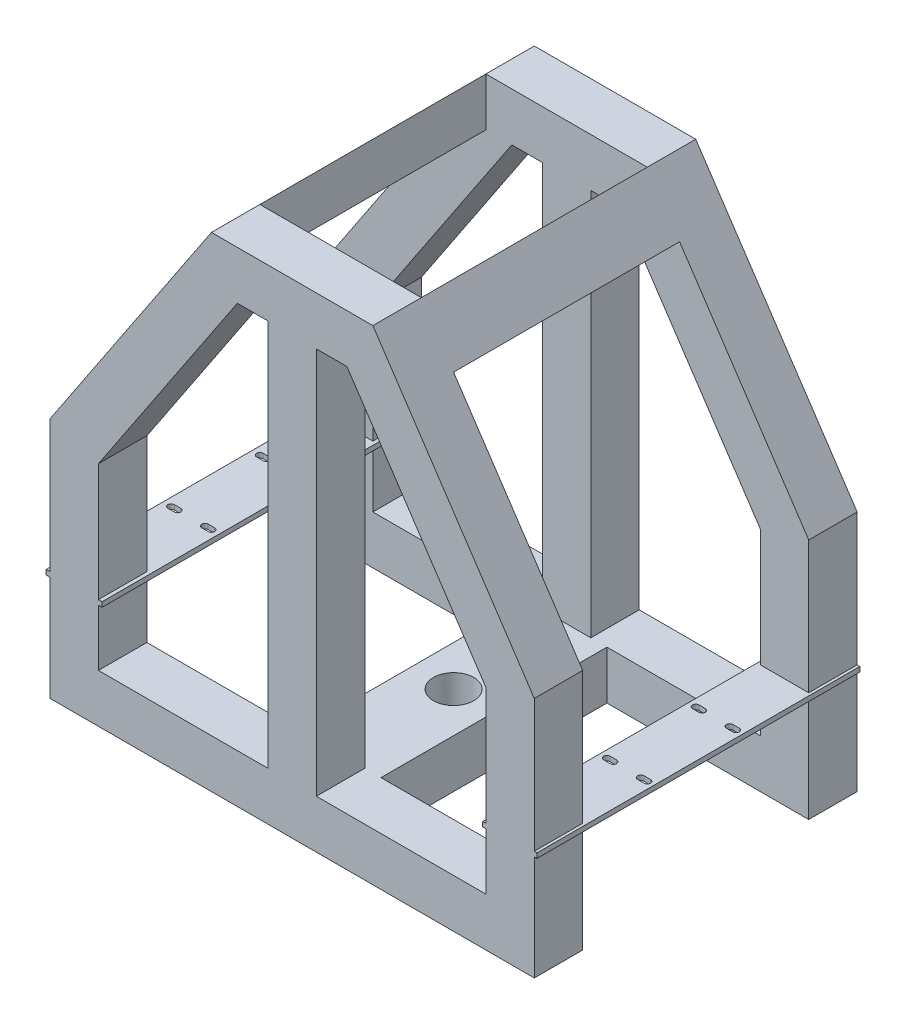
SolidWorks part; units mm, degrees
ref_plane "Front Plane" through (0, 0, 0) normal (0, 0, 1) x (1, 0, 0)
ref_plane "Top Plane" through (0, 0, 0) normal (0, 1, 0) x (1, 0, 0)
ref_plane "Right Plane" through (0, 0, 0) normal (1, 0, 0) x (0, 0, -1)
sketch "Sketch1" plane through (0, 0, 0) normal (0, 0, 1) x (1, 0, 0)
  line L0 (16.8622, -146.019) -> (16.8622, -177.0228) construction
  line L1 (66.8622, 153.981) -> (-33.1378, 153.981) construction
  line L2 (-33.1378, 153.981) -> (-133.1378, 3.981) construction
  line L3 (-133.1378, 3.981) -> (-133.1378, -146.019) construction
  line L4 (-133.1378, -146.019) -> (166.8622, -146.019) construction
  line L5 (1.8622, 153.981) -> (-33.1378, 153.981)
  line L6 (1.8622, -46.019) -> (31.8622, -46.019)
  line L7 (1.8622, -116.019) -> (1.8622, 123.981)
  line L8 (1.8622, 153.981) -> (31.8622, 153.981)
  line L9 (31.8622, -46.019) -> (31.8622, 153.981)
  line L10 (16.8622, 153.981) -> (16.8622, 166.0651) construction
  line L11 (16.8622, 166.0651) -> (16.8622, -345.3513) construction
  line L13 (-133.1378, 3.981) -> (-133.1378, -146.019)
  line L14 (-133.1378, -146.019) -> (-53.1378, -146.019)
  line L15 (-103.1378, -5.1022) -> (-103.1378, -116.019)
  line L16 (-33.1378, 153.981) -> (-133.1378, 3.981)
  line L17 (-133.1378, -146.019) -> (166.8622, -146.019)
  line L18 (166.8622, 3.981) -> (166.8622, -146.019) construction
  line L19 (66.8622, 153.981) -> (-33.1378, 153.981)
  line L20 (-17.0822, 123.981) -> (-103.1378, -5.1022)
  line L21 (1.8622, 123.981) -> (-17.0822, 123.981)
  line L22 (-103.1378, -5.1022) -> (-103.1378, -116.019)
  line L23 (-103.1378, -116.019) -> (1.8622, -116.019)
  line L24 (-8.1763, 137.34) -> (-108.1763, -12.66) construction
  line L25 (1.8622, 123.981) -> (-33.1378, 123.981) construction
  line L26 (-103.1378, 3.981) -> (-103.1378, -146.019) construction
  line L27 (66.8622, 153.981) -> (166.8622, 3.981) construction
  line L28 (136.8622, -116.019) -> (31.8622, -116.019)
  line L29 (136.8622, -5.1022) -> (136.8622, -116.019)
  line L30 (31.8622, 123.981) -> (50.8067, 123.981)
  line L31 (50.8067, 123.981) -> (136.8622, -5.1022)
  line L32 (66.8622, 153.981) -> (166.8622, 3.981)
  line L33 (136.8622, -5.1022) -> (136.8622, -116.019)
  line L34 (166.8622, -146.019) -> (86.8622, -146.019)
  line L35 (166.8622, 3.981) -> (166.8622, -146.019)
  line L36 (1.8622, -46.019) -> (1.8622, 153.981)
  line L37 (31.8622, -116.019) -> (31.8622, 123.981)
  line L38 (31.8622, 153.981) -> (66.8622, 153.981)
  point P4 (16.8622, -46.019)
  dimension "D1" = 150
  dimension "D2" = 150
  dimension "D3" = 150
  dimension "D4" = 150
  dimension "D5" = 50
  dimension "D6" = 30
  dimension "D9" = 30
  dimension "D8" = 30
extrude "Boss-Extrude4" add sketch "Sketch1" along normal blind 200 contours L28 L37 L6 L7 L23 L15 L20 L21 L36 L5 L16 L13 L14 L17 L35 L32 L19 L9 L30 L31 L29 | L36 L7 L6 L9 L8
sketch "Sketch5" plane through (0, -146.019, 0) normal (0, -1, 0) x (1, 0, 0)
  line L0 (-133.1378, 200) -> (-133.1378, 0) construction
  line L1 (-133.1378, 170) -> (166.8622, 170)
  line L2 (-133.1378, 170) -> (-133.1378, 30)
  line L3 (-133.1378, 30) -> (166.8622, 30)
  line L4 (166.8622, 170) -> (166.8622, 30)
  line L5 (166.8622, 200) -> (166.8622, 0) construction
  line L6 (-133.1378, 200) -> (166.8622, 200) construction
  line L7 (-133.1378, 0) -> (166.8622, 0) construction
  dimension "D1" = 30
  dimension "D2" = 30
extrude "Cut-Extrude3" cut sketch "Sketch5" against normal blind 270
sketch "Sketch6" plane through (0, 0, 200) normal (0, 0, 1) x (1, 0, 0)
  line L0 (-133.1378, 3.981) -> (-133.1378, -146.019) construction
  line L1 (-133.1378, -81.019) -> (-103.1378, -81.019)
  line L3 (-133.1378, -78.019) -> (-103.1378, -78.019)
  line L5 (-103.1378, -5.1022) -> (-103.1378, -116.019) construction
  line L6 (136.8622, -5.1022) -> (136.8622, -116.019) construction
  line L7 (136.8622, -81.019) -> (166.8622, -81.019)
  line L9 (136.8622, -78.019) -> (166.8622, -78.019)
  line L11 (166.8622, 3.981) -> (166.8622, -146.019) construction
  line L12 (-133.1378, -146.019) -> (166.8622, -146.019) construction
  line L14 (-135.5496, -78.019) -> (-100.8938, -78.019)
  line L15 (-135.5496, -78.019) -> (-135.5496, -81.019)
  line L16 (-135.5496, -81.019) -> (-100.8938, -81.019)
  line L17 (-100.8938, -78.019) -> (-100.8938, -81.019)
  line L18 (134.9079, -78.019) -> (168.5403, -78.019)
  line L19 (134.9079, -78.019) -> (134.9079, -81.019)
  line L20 (134.9079, -81.019) -> (168.5403, -81.019)
  line L21 (168.5403, -78.019) -> (168.5403, -81.019)
  point P18 (151.8622, -78.019)
  line M8 (136.8622, -5.1022) -> (136.8622, -116.019)
  line M13 (-133.1378, 3.981) -> (-133.1378, -146.019)
  line M15 (166.8622, -146.019) -> (166.8622, 3.981)
  line M19 (-103.1378, -116.019) -> (-103.1378, -5.1022)
  dimension "D1" = 68
  dimension "D2" = 68
  dimension "D3" = 3
  dimension "D4" = 3
extrude "Boss-Extrude6" add sketch "Sketch6" against normal blind 200 contours L15 L16 L14 M13 | L3 L1 M13 M19 | L17 L14 L16 M19 | L9 L7 M8 M15 | L21 L18 L20 M15 | L19 L20 L18 M8
sketch "Sketch7" plane through (0, 153.981, 0) normal (0, 1, 0) x (1, 0, 0)
  line L0 (-33.1378, -200) -> (-33.1378, 0) construction
  line L1 (-33.1378, -30) -> (66.8622, -30)
  line L2 (-33.1378, -30) -> (-33.1378, -170)
  line L3 (-33.1378, -170) -> (66.8622, -170)
  line L4 (66.8622, -30) -> (66.8622, -170)
  line L5 (66.8622, -200) -> (66.8622, 0) construction
extrude "Cut-Extrude4" cut sketch "Sketch7" against normal blind 174
sketch "Sketch9" plane through (0, 0, 0) normal (0, 0, -1) x (-1, 0, 0)
  line L0 (-136.8622, -116.019) -> (-31.8622, -116.019) construction
  line L1 (-41.8622, -116.019) -> (8.1378, -116.019)
  line L2 (-41.8622, -116.019) -> (-41.8622, -146.019)
  line L3 (-41.8622, -146.019) -> (8.1378, -146.019)
  line L4 (8.1378, -116.019) -> (8.1378, -146.019)
  line L5 (133.1378, -146.019) -> (-166.8622, -146.019) construction
  line L6 (-31.8622, -116.019) -> (-31.8622, 123.981) construction
  dimension "D1" = 50
  dimension "D2" = 10
extrude "Boss-Extrude7" add sketch "Sketch9" against normal blind 193
sketch "Sketch10" plane through (0, -146.019, 0) normal (0, -1, 0) x (1, 0, 0)
  line L0 (-8.1378, 170) -> (-133.1378, 170) construction
  line L4 (-133.1378, 30) -> (-8.1378, 30) construction
  line L5 (-8.1378, 170) -> (-8.1378, 30) construction
  circle A0 centre (16.8622, 100) radius 12.5
  dimension "D3" = 25
  dimension "D1" = 140
  dimension "D2" = 25
extrude "Cut-Extrude5" cut sketch "Sketch10" against normal blind 193
sketch "Sketch11" plane through (0, -78.019, 0) normal (0, 1, 0) x (1, 0, 0)
  line L0 (139.3622, -127.5) -> (143.3622, -127.5) construction
  line L3 (151.8622, -170) -> (151.8622, 30) construction
  line L4 (166.8622, -170) -> (136.8622, -170) construction
  line L5 (136.8622, -100) -> (166.8622, -100) construction
  line L6 (136.8622, -30) -> (136.8622, -170) construction
  line L7 (166.8622, -30) -> (166.8622, -170) construction
  line L8 (139.3622, -125.5) -> (143.3622, -125.5)
  line L9 (139.3622, -129.5) -> (143.3622, -129.5)
  line L10 (164.3622, -127.5) -> (160.3622, -127.5) construction
  line L11 (164.3622, -125.5) -> (160.3622, -125.5)
  line L12 (164.3622, -129.5) -> (160.3622, -129.5)
  line L13 (164.3622, -72.5) -> (160.3622, -72.5) construction
  line L14 (164.3622, -74.5) -> (160.3622, -74.5)
  line L15 (164.3622, -70.5) -> (160.3622, -70.5)
  line L16 (139.3622, -72.5) -> (143.3622, -72.5) construction
  line L17 (139.3622, -74.5) -> (143.3622, -74.5)
  line L18 (139.3622, -70.5) -> (143.3622, -70.5)
  line L19 (16.8622, 8.2373) -> (16.8622, -220.4395) construction
  line L20 (-130.6378, -127.5) -> (-126.6378, -127.5) construction
  line L21 (-130.6378, -125.5) -> (-126.6378, -125.5)
  line L22 (-130.6378, -129.5) -> (-126.6378, -129.5)
  line L23 (-105.6378, -127.5) -> (-109.6378, -127.5) construction
  line L24 (-105.6378, -125.5) -> (-109.6378, -125.5)
  line L25 (-105.6378, -129.5) -> (-109.6378, -129.5)
  line L26 (-130.6378, -72.5) -> (-126.6378, -72.5) construction
  line L27 (-130.6378, -74.5) -> (-126.6378, -74.5)
  line L28 (-130.6378, -70.5) -> (-126.6378, -70.5)
  line L29 (-105.6378, -72.5) -> (-109.6378, -72.5) construction
  line L30 (-105.6378, -74.5) -> (-109.6378, -74.5)
  line L31 (-105.6378, -70.5) -> (-109.6378, -70.5)
  arc A2 (139.3622, -125.5) -> (139.3622, -129.5) centre (139.3622, -127.5) ccw
  arc A3 (143.3622, -129.5) -> (143.3622, -125.5) centre (143.3622, -127.5) ccw
  arc A4 (164.3622, -125.5) -> (164.3622, -129.5) centre (164.3622, -127.5) cw
  arc A5 (160.3622, -129.5) -> (160.3622, -125.5) centre (160.3622, -127.5) cw
  arc A6 (164.3622, -74.5) -> (164.3622, -70.5) centre (164.3622, -72.5) ccw
  arc A7 (160.3622, -70.5) -> (160.3622, -74.5) centre (160.3622, -72.5) ccw
  arc A8 (139.3622, -74.5) -> (139.3622, -70.5) centre (139.3622, -72.5) cw
  arc A9 (143.3622, -70.5) -> (143.3622, -74.5) centre (143.3622, -72.5) cw
  arc A10 (-130.6378, -125.5) -> (-130.6378, -129.5) centre (-130.6378, -127.5) ccw
  arc A11 (-126.6378, -129.5) -> (-126.6378, -125.5) centre (-126.6378, -127.5) ccw
  arc A12 (-105.6378, -125.5) -> (-105.6378, -129.5) centre (-105.6378, -127.5) cw
  arc A13 (-109.6378, -129.5) -> (-109.6378, -125.5) centre (-109.6378, -127.5) cw
  arc A14 (-130.6378, -74.5) -> (-130.6378, -70.5) centre (-130.6378, -72.5) cw
  arc A15 (-126.6378, -70.5) -> (-126.6378, -74.5) centre (-126.6378, -72.5) cw
  arc A16 (-105.6378, -74.5) -> (-105.6378, -70.5) centre (-105.6378, -72.5) ccw
  arc A17 (-109.6378, -70.5) -> (-109.6378, -74.5) centre (-109.6378, -72.5) ccw
  point P2 (141.3622, -127.5)
  point P19 (162.3622, -127.5)
  point P26 (162.3622, -72.5)
  point P33 (141.3622, -72.5)
  point P42 (-128.6378, -127.5)
  point P49 (-107.6378, -127.5)
  point P56 (-128.6378, -72.5)
  point P63 (-107.6378, -72.5)
  dimension "D2" = 2
  dimension "D4" = 4
  dimension "D1" = 27.5
  dimension "D3" = 200
  dimension "D5" = 8.5
extrude "Cut-Extrude23" cut sketch "Sketch11" against normal blind 10
sketch "Sketch12" plane through (0, -146.019, 0) normal (0, -1, 0) x (1, 0, 0)
  line L0 (-133.1378, 200) -> (166.8622, 200) construction
  line L1 (168.5403, 0) -> (168.5403, 200) construction
  circle A0 centre (18.5403, 250) radius 50
  dimension "D1" = 100
  dimension "D2" = 50
  dimension "D3" = 150
